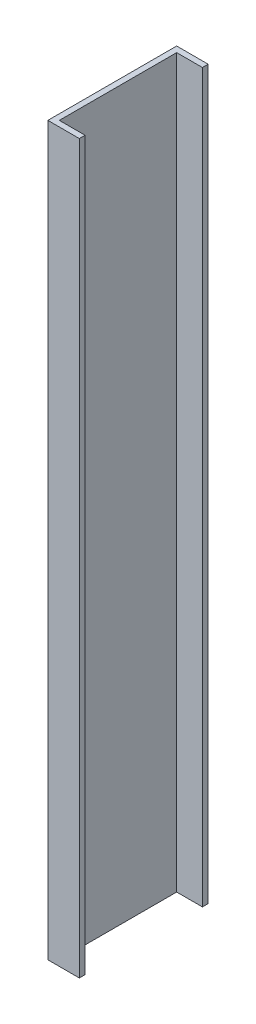
SolidWorks part; units mm, degrees
ref_plane "Front Plane" through (0, 0, 0) normal (0, 0, 1) x (1, 0, 0)
ref_plane "Top Plane" through (0, 0, 0) normal (0, 1, 0) x (1, 0, 0)
ref_plane "Right Plane" through (0, 0, 0) normal (1, 0, 0) x (0, 0, -1)
sketch "Sketch1" plane through (0, 0, 0) normal (0, 1, 0) x (1, 0, 0)
  line L0 (0, 0) -> (0, 45)
  line L1 (0, 45) -> (11, 45)
  line L2 (11, 45) -> (11, 43)
  line L3 (11, 43) -> (2, 43)
  line L4 (2, 43) -> (2, 2)
  line L5 (2, 2) -> (11, 2)
  line L6 (11, 2) -> (11, 0)
  line L7 (11, 0) -> (0, 0)
  line L8 (11, 2) -> (11, 43) construction
  line L9 (0, 22.5) -> (2, 22.5) construction
  dimension "D1" = 45
  dimension "D2" = 2
  dimension "D3" = 11
extrude "Boss-Extrude1" add sketch "Sketch1" along normal blind 254
